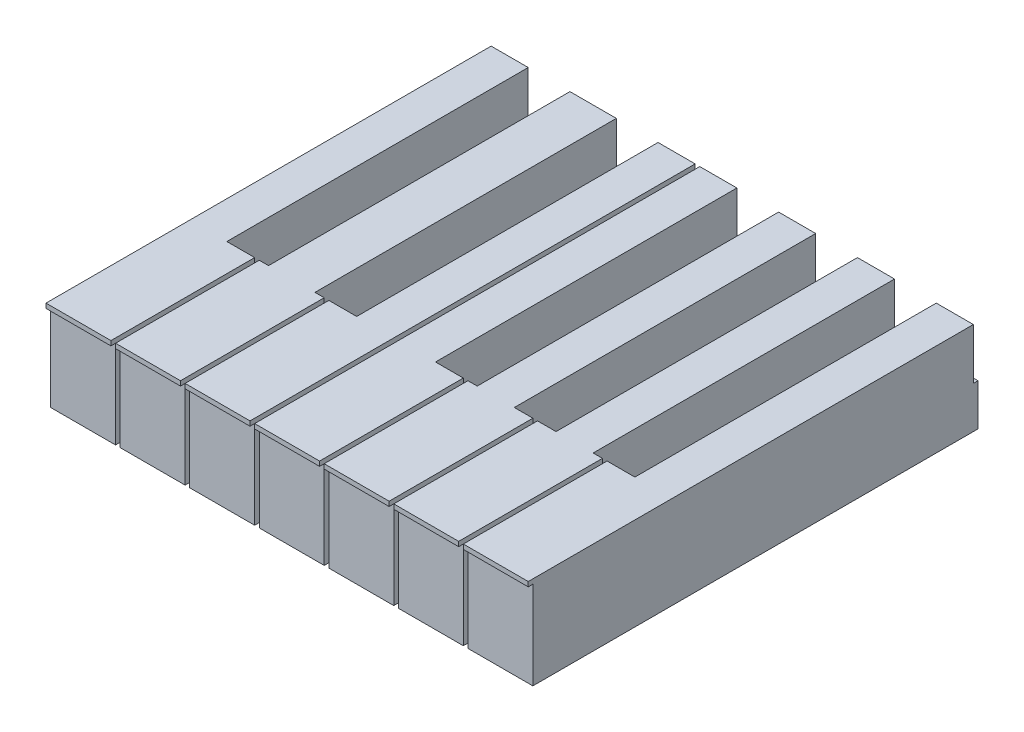
SolidWorks part; units mm, degrees
material "PE High Density Film"
ref_plane "Front Plane" through (0, 0, 0) normal (0, 0, 1) x (1, 0, 0)
ref_plane "Top Plane" through (0, 0, 0) normal (0, 1, 0) x (1, 0, 0)
ref_plane "Right Plane" through (0, 0, 0) normal (1, 0, 0) x (0, 0, -1)
sketch "Sketch1" plane through (0, 0, 0) normal (0, 1, 0) x (1, 0, 0)
  line L0 (0, 0) -> (0, 152.4)
  line L1 (0, 152.4) -> (12.7, 152.4)
  line L2 (12.7, 152.4) -> (12.7, 49.2125)
  line L3 (12.7, 49.2125) -> (22.225, 49.2125)
  line L4 (22.225, 49.2125) -> (22.225, 0)
  line L5 (22.225, 0) -> (0, 0)
  line L6 (23.8125, 49.2125) -> (26.9875, 49.2125)
  line L7 (26.9875, 49.2125) -> (26.9875, 152.4)
  line L8 (26.9875, 152.4) -> (42.8625, 152.4)
  line L9 (42.8625, 152.4) -> (42.8625, 49.2125)
  line L10 (42.8625, 49.2125) -> (46.0375, 49.2125)
  line L11 (46.0375, 49.2125) -> (46.0375, 0)
  line L12 (46.0375, 0) -> (23.8125, 0)
  line L13 (23.8125, 0) -> (23.8125, 49.2125)
  line L14 (47.625, 49.2125) -> (57.15, 49.2125)
  line L15 (57.15, 49.2125) -> (57.15, 152.4)
  line L16 (57.15, 152.4) -> (69.85, 152.4)
  line L17 (69.85, 152.4) -> (69.85, 0)
  line L18 (69.85, 0) -> (47.625, 0)
  line L19 (47.625, 0) -> (47.625, 49.2125)
  line L20 (71.4375, 152.4) -> (71.4375, 0)
  line L21 (71.4375, 0) -> (93.6625, 0)
  line L22 (93.6625, 0) -> (93.6625, 49.2125)
  line L23 (93.6625, 49.2125) -> (84.1375, 49.2125)
  line L24 (84.1375, 49.2125) -> (84.1375, 152.4)
  line L25 (84.1375, 152.4) -> (71.4375, 152.4)
  line L26 (95.25, 0) -> (95.25, 49.2125)
  line L27 (95.25, 49.2125) -> (98.425, 49.2125)
  line L28 (98.425, 49.2125) -> (98.425, 152.4)
  line L29 (98.425, 152.4) -> (111.125, 152.4)
  line L31 (117.475, 0) -> (95.25, 0)
  line L32 (111.125, 152.4) -> (111.125, 49.2125)
  line L33 (111.125, 49.2125) -> (117.475, 49.2125)
  line L34 (117.475, 49.2125) -> (117.475, 0)
  line L35 (119.0625, 49.2125) -> (125.4125, 49.2125)
  line L36 (125.4125, 49.2125) -> (125.4125, 152.4)
  line L37 (125.4125, 152.4) -> (138.1125, 152.4)
  line L38 (138.1125, 152.4) -> (138.1125, 49.2125)
  line L39 (138.1125, 49.2125) -> (141.2875, 49.2125)
  line L40 (141.2875, 49.2125) -> (141.2875, 0)
  line L41 (141.2875, 0) -> (119.0625, 0)
  line L42 (119.0625, 0) -> (119.0625, 49.2125)
  line L43 (142.875, 49.2125) -> (152.4, 49.2125)
  line L44 (152.4, 49.2125) -> (152.4, 152.4)
  line L45 (152.4, 152.4) -> (165.1, 152.4)
  line L46 (165.1, 152.4) -> (165.1, 0)
  line L47 (165.1, 0) -> (142.875, 0)
  line L48 (142.875, 0) -> (142.875, 49.2125)
  dimension "D1" = 152.4
  dimension "D2" = 103.1875
  dimension "D3" = 14.2875
  dimension "D4" = 1.5875
  dimension "D5" = 9.525
  dimension "D6" = 22.225
  dimension "D7" = 9.525
  dimension "D8" = 1.5875
  dimension "D9" = 14.2875
  dimension "D10" = 9.525
  dimension "D11" = 1.5875
  dimension "D12" = 14.2875
  dimension "D13" = 1.5875
  dimension "D14" = 1.5875
  dimension "D15" = 14.2875
  dimension "D16" = 1.5875
  dimension "D17" = 14.2875
  dimension "D18" = 9.525
extrude "Boss-Extrude1" add sketch "Sketch1" along normal blind 31.75
sketch "Sketch2" plane through (0, 0, 0) normal (-1, 0, 0) x (0, 0, 1)
  line L0 (0, 30.1625) -> (-1.5875, 30.1625)
  line L1 (0, 31.75) -> (0, 0) construction
  line L2 (-1.5875, 30.1625) -> (-1.5875, 0)
  line L3 (-152.4, 0) -> (0, 0) construction
  line L4 (-1.5875, 0) -> (0, 0)
  line L5 (0, 0) -> (0, 30.1625)
  line L6 (-152.4, 31.75) -> (0, 31.75) construction
  dimension "D1" = 1.5875
  dimension "D2" = 1.5875
extrude "Cut-Extrude1" cut sketch "Sketch2" against normal through all
sketch "Sketch4" plane through (0, 0, 0) normal (1, 0, 0) x (0, 0, -1)
  line L1 (152.4, 0) -> (153.9875, 0)
  line L2 (152.4, 0) -> (152.4, 14.2875)
  line L3 (152.4, 14.2875) -> (153.9875, 14.2875)
  line L4 (153.9875, 0) -> (153.9875, 14.2875)
  dimension "D1" = 14.2875
  dimension "D2" = 1.5875
extrude "Boss-Extrude2" add sketch "Sketch4" along normal through all
